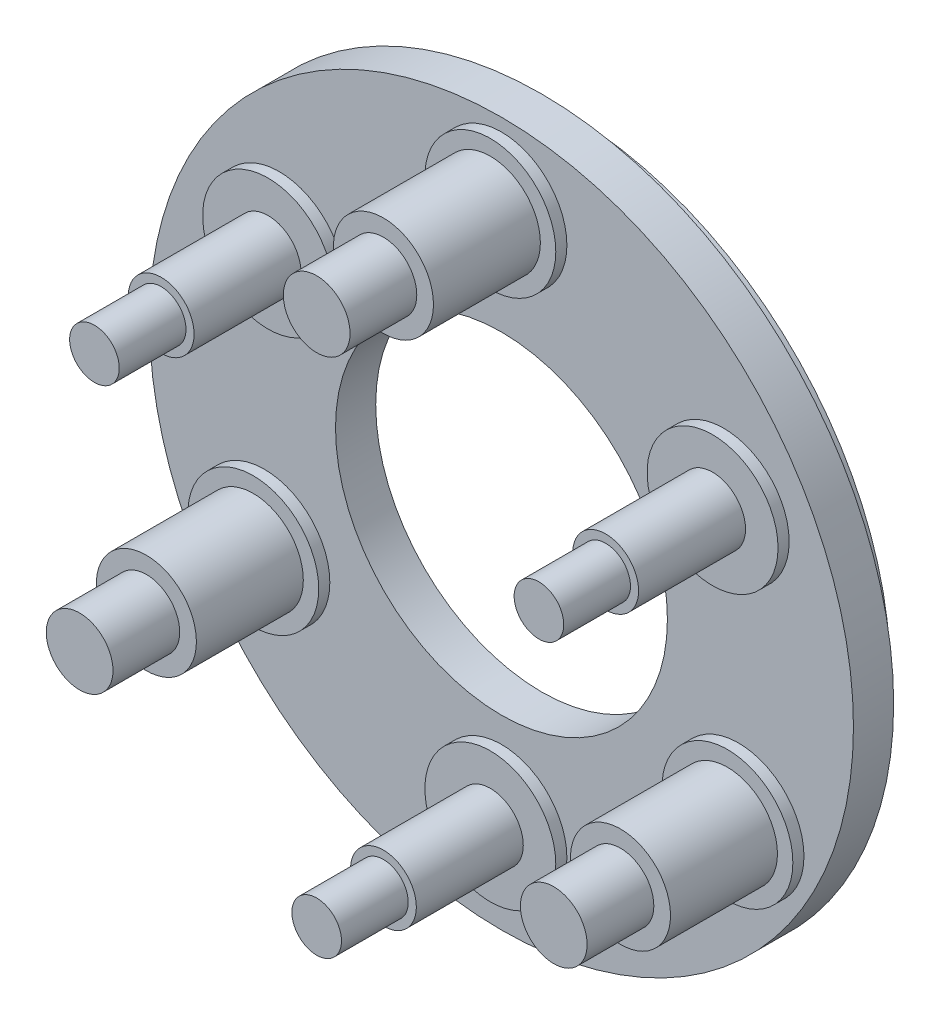
SolidWorks part; units mm, degrees
material "PET"
ref_plane "Front Plane" through (0, 0, 0) normal (0, 0, 1) x (1, 0, 0)
ref_plane "Top Plane" through (0, 0, 0) normal (0, 1, 0) x (1, 0, 0)
ref_plane "Right Plane" through (0, 0, 0) normal (1, 0, 0) x (0, 0, -1)
sketch "Sketch1" plane through (0, 0, 0) normal (0, 0, 1) x (1, 0, 0)
  circle A0 centre (0, 0) radius 10.4521
  circle A1 centre (0, 0) radius 4.9276
  dimension "D1" = 20.9042
  dimension "D2" = 9.8552
extrude "Base" add sketch "Sketch1" along normal blind 1.1938
sketch "Sketch2" plane through (0, 0, 0) normal (0, 0, -1) x (-1, 0, 0)
  circle A0 centre (0, 0) radius 9.6393
  circle A1 centre (0, 0) radius 8.89
  dimension "D1" = 17.78
  dimension "D2" = 0.7493
extrude "Track" add sketch "Sketch2" along normal blind 0.7112
sketch "Sketch3" plane through (0, 0, 1.1938) normal (0, 0, 1) x (1, 0, 0)
  line L0 (0, 0) -> (0, 10.4521) construction
  line L1 (0, 10.4521) -> (0, -10.4521) construction
  circle A0 centre (0, 0) radius 10.4521 construction
  circle A1 centre (0, 8.128) radius 1.9431
  circle A2 centre (0, -7.62) radius 1.9431
  dimension "D1" = 3.8862
  dimension "D3" = 3.8862
  dimension "D2" = 8.128
  dimension "D4" = 7.62
extrude "Platform 1" add sketch "Sketch3" along normal blind 0.3302
sketch "Sketch4" plane through (0, 0, 1.524) normal (0, 0, 1) x (1, 0, 0)
  circle A0 centre (0, 8.128) radius 1.4859
  circle A1 centre (0, -7.62) radius 0.9779
  dimension "D1" = 2.9718
  dimension "D2" = 1.9558
extrude "Platform 2" add sketch "Sketch4" along normal blind 3.175
sketch "Sketch5" plane through (0, 0, 4.699) normal (0, 0, 1) x (1, 0, 0)
  circle A0 centre (0, 8.128) radius 0.9906
  circle A1 centre (0, -7.62) radius 0.7366
  dimension "D1" = 1.9812
  dimension "D2" = 1.4732
extrude "Platform 3" add sketch "Sketch5" along normal blind 1.9812
pattern_circular "CirPattern1" count 3 over 360 about axis through (0, 0, 0) along (0, 0, 1) of "Platform 1", "Platform 2", "Platform 3"
equation "\"D3@Sketch3\"=\"D1@Sketch3\""
